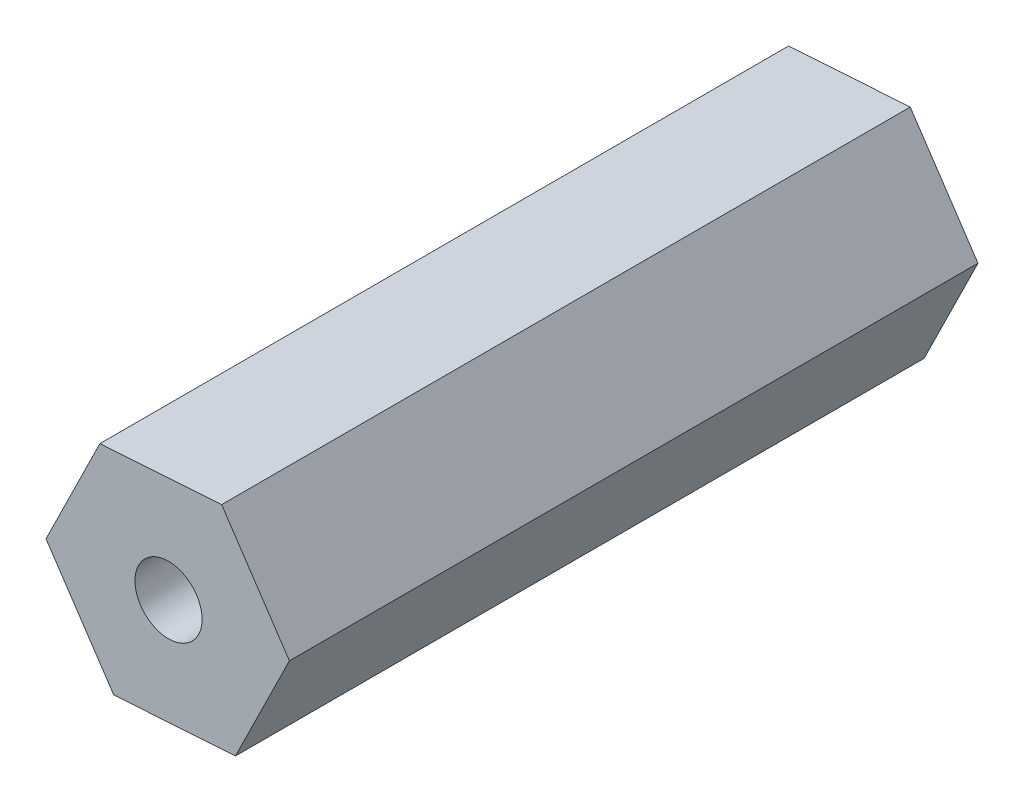
SolidWorks part; units mm, degrees
ref_plane "Front Plane" through (0, 0, 0) normal (0, 0, 1) x (1, 0, 0)
ref_plane "Top Plane" through (0, 0, 0) normal (0, 1, 0) x (1, 0, 0)
ref_plane "Right Plane" through (0, 0, 0) normal (1, 0, 0) x (0, 0, -1)
sketch "Sketch1" plane through (0, 0, 0) normal (0, 0, 1) x (1, 0, 0)
  line L1 (3.2424, 6.5765) -> (-4.0742, 6.0962)
  line L2 (-4.0742, 6.0962) -> (-7.3166, -0.4803)
  line L3 (-7.3166, -0.4803) -> (-3.2424, -6.5765)
  line L4 (-3.2424, -6.5765) -> (4.0742, -6.0962)
  line L5 (4.0742, -6.0962) -> (7.3166, 0.4803)
  line L6 (7.3166, 0.4803) -> (3.2424, 6.5765)
  circle A0 centre (0, 0) radius 6.35 construction
  dimension "D1" = 12.7
extrude "Boss-Extrude1" add sketch "Sketch1" along normal blind 41.402
sketch "Sketch2" plane through (0, 0, 41.402) normal (0, 0, 1) x (1, 0, 0)
  line L0 (-3.2424, -6.5765) -> (4.0742, -6.0962) construction
  circle A0 centre (0.0494, 0.0136) radius 2.0193
  point P2 (0.4159, -6.3364)
  dimension "D1" = 7.366
  dimension "D3" = 4.0386
  dimension "D2" = 6.35
extrude "Cut-Extrude2" cut sketch "Sketch2" against normal blind 12.7 contours A0
sketch "Sketch3" plane through (0, 0, 0) normal (0, 0, -1) x (-1, 0, 0)
  line L0 (3.2424, -6.5765) -> (-4.0742, -6.0962) construction
  circle A0 centre (0.0494, -0.0032) radius 1.8428
  dimension "D1" = 7.366
  dimension "D2" = 6.35
extrude "Cut-Extrude7" cut sketch "Sketch3" against normal blind 12.7
